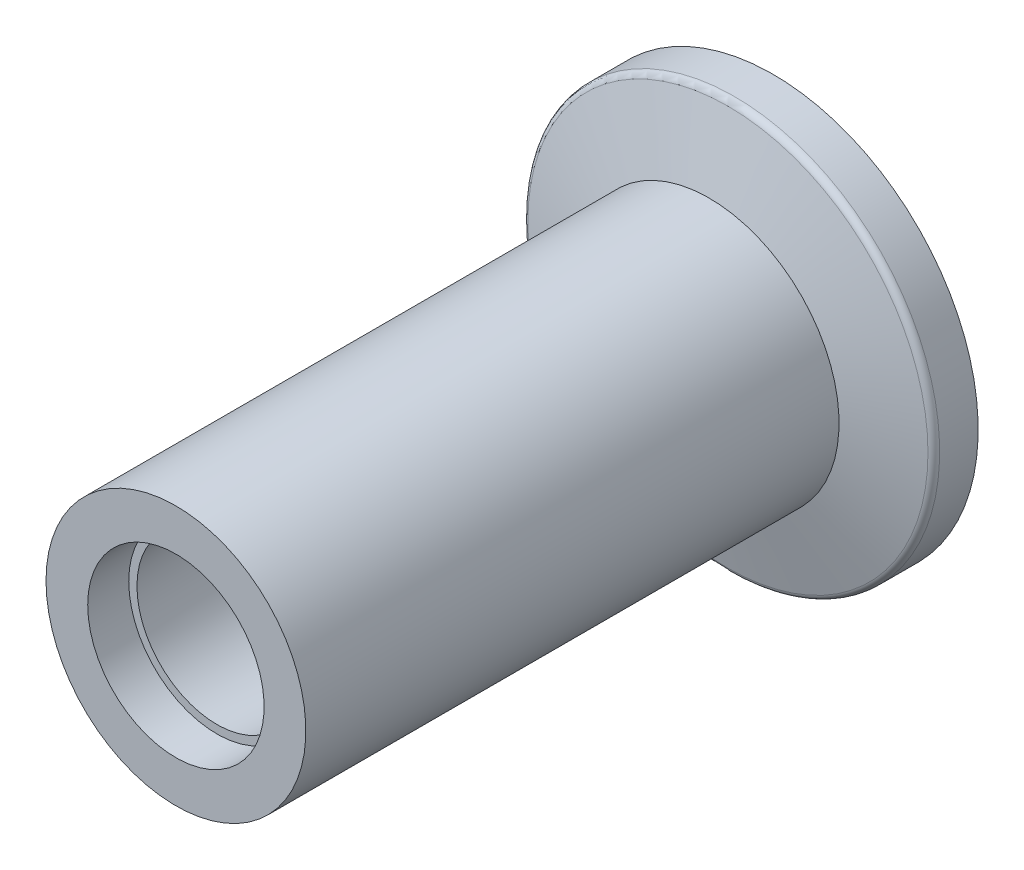
SolidWorks part; units mm, degrees
ref_plane "Front Plane" through (0, 0, 0) normal (0, 0, 1) x (1, 0, 0)
ref_plane "Top Plane" through (0, 0, 0) normal (0, 1, 0) x (1, 0, 0)
ref_plane "Right Plane" through (0, 0, 0) normal (1, 0, 0) x (0, 0, -1)
ref_plane "Plane1" through (0, 0, 0) normal (0, -1, 0) x (1, 0, 0)
sketch "Sketch1" plane through (0, 0, 0) normal (0, -1, 0) x (1, 0, 0)
  line L0 (9.7, 2.502) -> (9.7, 12.002)
  line L1 (8.05, 0.3283) -> (6.05, 38.4906)
  line L3 (0.2, 11.872) -> (0.2, -16.2294) construction
  line L4 (9.2, -2.1717) -> (15.2, -2.1717)
  line L5 (15.2, -2.1717) -> (15.2, 0.6446)
  line L6 (14.8294, 1.1276) -> (9.7, 2.502)
  line L7 (0.2, -16.2294) -> (0.2, 48.5081) construction
  line L8 (9.7, 12.002) -> (9.7, 41.4906)
  line L9 (9.7, 41.4906) -> (6.65, 41.4906)
  line L10 (0.2, 11.872) -> (0.2, -11.872) construction
  line L11 (6.65, 41.4906) -> (6.65, 38.4906)
  line L12 (6.65, 38.4906) -> (6.05, 38.4906)
  line L13 (9.2, -2.1717) -> (9.2, 0.3283)
  line L14 (9.2, 0.3283) -> (8.05, 0.3283)
  arc A0 (15.2, 0.6446) -> (14.8294, 1.1276) centre (14.7, 0.6446) ccw
  point P17 (15.2, 1.0283)
  dimension "D18" = 0.5
  dimension "D2" = 9.5
  dimension "D3" = 6.45
  dimension "D4" = 28.1014
  dimension "D5" = 23.744
  dimension "D6" = 15
  dimension "D7" = 3
  dimension "D8" = 3.2
  dimension "D9" = 0.6
  dimension "D10" = 2.5
  dimension "D11" = 7.85
  dimension "D12" = 6
  dimension "D13" = 15
  dimension "D14" = 75
  dimension "D15" = 9.5
  dimension "D16" = 1.15
  dimension "D17" = 3
revolve "Revolve1" add sketch "Sketch1" angle 360 about L10
